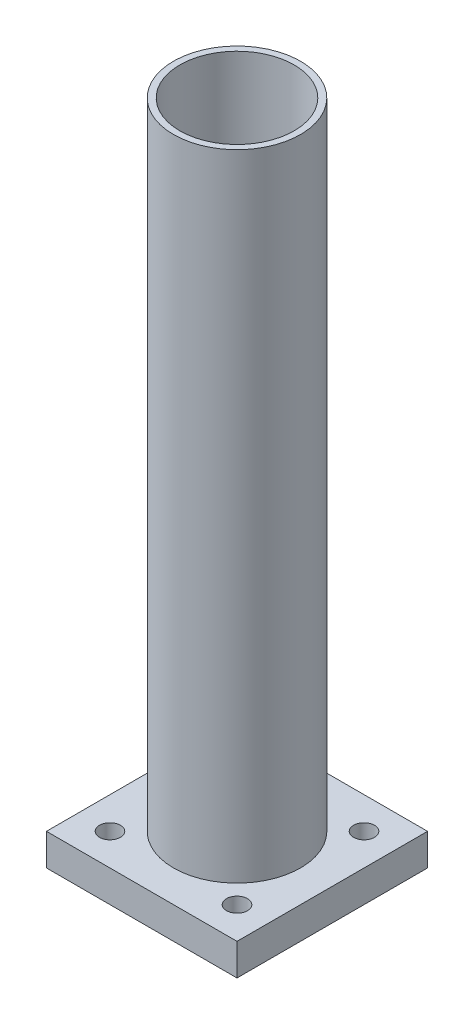
SolidWorks part; units mm, degrees
material "AISI 304"
ref_plane "前视基准面" through (0, 0, 0) normal (0, 0, 1) x (1, 0, 0)
ref_plane "上视基准面" through (0, 0, 0) normal (0, 1, 0) x (1, 0, 0)
ref_plane "右视基准面" through (0, 0, 0) normal (1, 0, 0) x (0, 0, -1)
sketch "Sketch1" plane through (0, 0, 0) normal (0, 1, 0) x (1, 0, 0)
  circle A0 centre (0, 0) radius 20
  circle A1 centre (0, 0) radius 18
  dimension "D1" = 40
  dimension "D2" = 2
extrude "Boss-Extrude1" add sketch "Sketch1" along normal blind 200
sketch "Sketch2" plane through (0, 0, 0) normal (0, 1, 0) x (1, 0, 0)
  line L1 (30, -30) -> (-30, -30)
  line L2 (30, -30) -> (30, 30)
  line L3 (30, 30) -> (-30, 30)
  line L4 (-30, -30) -> (-30, 30)
  line L5 (30, -30) -> (-30, 30) construction
  line L6 (30, 30) -> (-30, -30) construction
  point P0 (0, 0)
  dimension "D1" = 60
extrude "Boss-Extrude2" add sketch "Sketch2" against normal blind 10 separate body
hole_wizard "M6 Clearance Hole1" positions "Sketch3" profile "Sketch5" hole size "M6" standard "GB" end condition through all
sketch "Sketch3" plane through (0, 0, 0) normal (0, 1, 0) x (1, 0, 0)
  line L0 (0, -33) -> (0, 33) construction
  line L1 (-33, 0) -> (33, 0) construction
  point P0 (20, 20)
  point P5 (-20, 20)
  point P8 (-20, -20)
  point P9 (20, -20)
  dimension "D1" = 20
  dimension "D2" = 20
sketch "Sketch5" plane through (20, 0, -20) normal (1, 0, 0) x (0, 0, 1)
  line L0 (0, 0) -> (0, 10)
  line L1 (0, 10) -> (3.3, 10)
  line L2 (3.3, 10) -> (3.3, 0)
  line L5 (3.3, 0) -> (0, 0)
  line L11 (0, -6.35) -> (0, 107.95) construction
  dimension "Thru Hole Dia." = 6.6
  dimension "Thru Hole Depth" = 10
